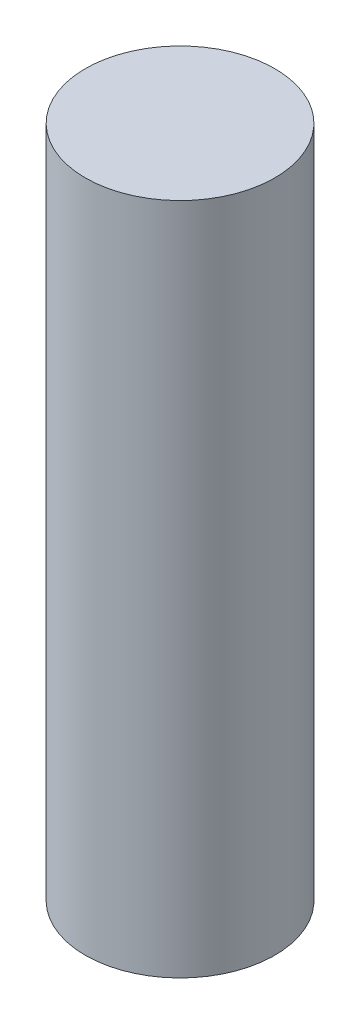
SolidWorks part; units mm, degrees
ref_plane "Front Plane" through (0, 0, 0) normal (0, 0, 1) x (1, 0, 0)
ref_plane "Top Plane" through (0, 0, 0) normal (0, 1, 0) x (1, 0, 0)
ref_plane "Right Plane" through (0, 0, 0) normal (1, 0, 0) x (0, 0, -1)
sketch "Sketch1" plane through (0, 0, 0) normal (0, 1, 0) x (1, 0, 0)
  circle A0 centre (0, 0) radius 9.15
  dimension "D1" = 18.3
extrude "Boss-Extrude1" add sketch "Sketch1" along normal blind 65.05
